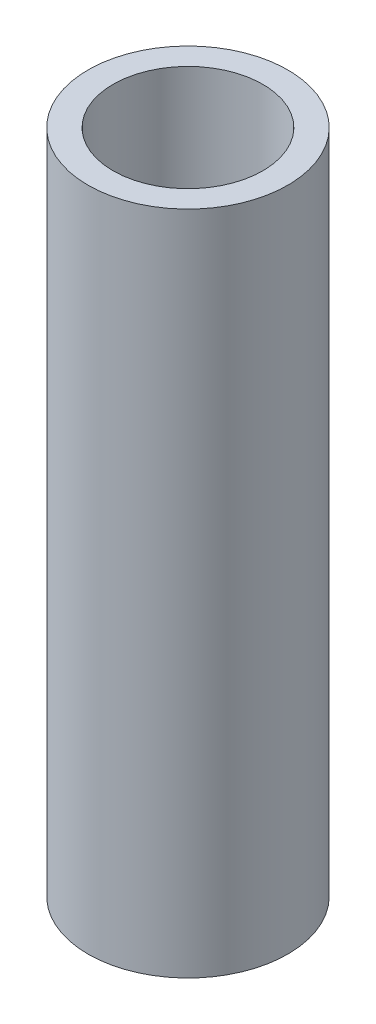
SolidWorks part; units mm, degrees
material "EPDM 60 Durometer"
ref_plane "Front Plane" through (0, 0, 0) normal (0, 0, 1) x (1, 0, 0)
ref_plane "Top Plane" through (0, 0, 0) normal (0, 1, 0) x (1, 0, 0)
ref_plane "Right Plane" through (0, 0, 0) normal (1, 0, 0) x (0, 0, -1)
sketch "Sketch1" plane through (0, 0, 0) normal (0, 1, 0) x (1, 0, 0)
  circle A0 centre (0, 0) radius 6
  dimension "D1" = 12
extrude "Boss-Extrude1" add sketch "Sketch1" along normal blind 40
sketch "Sketch2" plane through (0, 40, 0) normal (0, 1, 0) x (1, 0, 0)
  circle A0 centre (0, 0) radius 4.5
  dimension "D1" = 9
extrude "Cut-Extrude1" cut sketch "Sketch2" against normal blind 38
